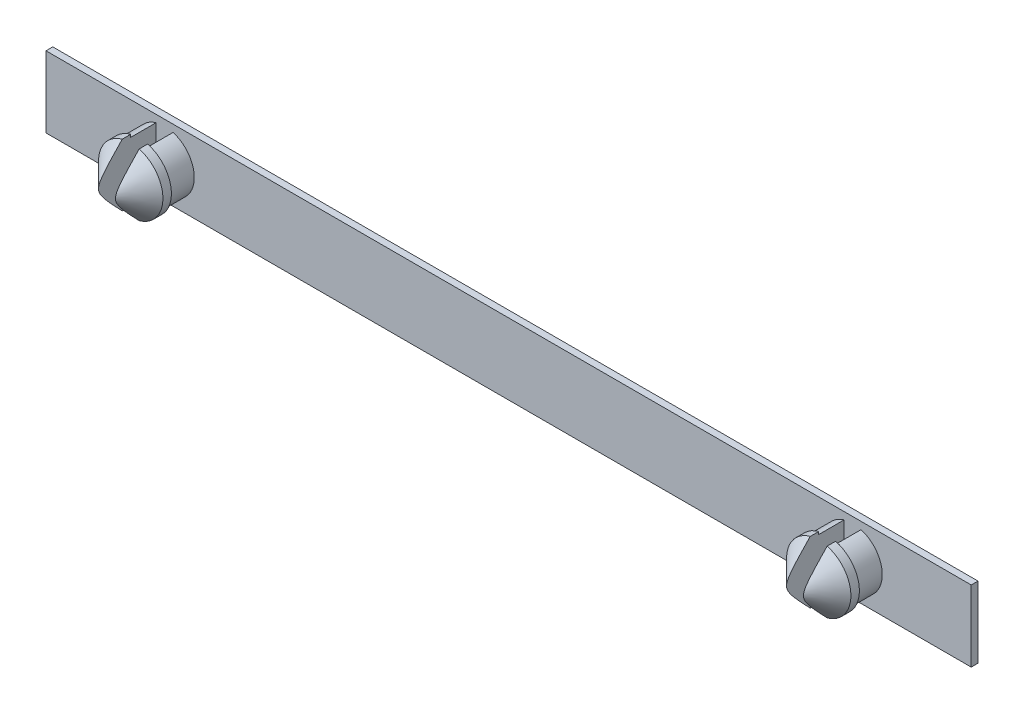
SolidWorks part; units mm, degrees
ref_plane "Přední rovina" through (0, 0, 0) normal (0, 0, 1) x (1, 0, 0)
ref_plane "Horní rovina" through (0, 0, 0) normal (0, 1, 0) x (1, 0, 0)
ref_plane "Pravá rovina" through (0, 0, 0) normal (1, 0, 0) x (0, 0, -1)
sketch "Skica2" plane through (0, 0, 0) normal (0, 0, 1) x (1, 0, 0)
  line L1 (-27.3, 2.1) -> (27.3, 2.1)
  line L2 (-27.3, 2.1) -> (-27.3, -2.1)
  line L3 (-27.3, -2.1) -> (27.3, -2.1)
  line L4 (27.3, 2.1) -> (27.3, -2.1)
  line L5 (-27.3, 2.1) -> (27.3, -2.1) construction
  line L6 (-27.3, -2.1) -> (27.3, 2.1) construction
  point P0 (0, 0)
  point P5 (-1, -0.2)
  dimension "D1" = 4.2
  dimension "D2" = 54.6
extrude "Přidat vysunutím2" add sketch "Skica2" along normal blind 0.4
sketch "Skica3" plane through (0, 0, 0.4) normal (0, 0, 1) x (1, 0, 0)
  line L0 (-27.3, 2.1) -> (-27.3, -2.1) construction
  line L1 (27.3, -2.1) -> (27.3, 2.1) construction
  line L2 (27.3, 2.1) -> (-27.3, 2.1) construction
  line L3 (-27.3, -2.1) -> (27.3, -2.1) construction
  circle A0 centre (-20.3, 0) radius 1.75
  circle A1 centre (20.3, 0) radius 1.75
  dimension "D1" = 3.5
  dimension "D3" = 3.5
  dimension "D2" = 7
  dimension "D4" = 7
  dimension "D5" = 2.1
  dimension "D6" = 2.1
  dimension "D7" = 2.1
extrude "Přidat vysunutím3" add sketch "Skica3" along normal blind 1.5
sketch "Skica5" plane through (0, 0, 1.9) normal (0, 0, 1) x (1, 0, 0)
  circle A0 centre (-20.3, 0) radius 1.9
  circle A1 centre (20.3, 0) radius 1.9
  dimension "D1" = 3.8
  dimension "D2" = 3.8
extrude "Přidat vysunutím5" add sketch "Skica5" along normal blind 2
chamfer "Zkosení2" distance 1.5 angle 45 2 edges at (22.2, 0, 3.9) (-18.4, 0, 3.9)
sketch "Skica7" plane through (0, 0, 3.9) normal (0, 0, 1) x (1, 0, 0)
  line L1 (-19.8, 2.5) -> (-20.8, 2.5)
  line L2 (-19.8, 2.5) -> (-19.8, -2.5)
  line L3 (-19.8, -2.5) -> (-20.8, -2.5)
  line L4 (-20.8, 2.5) -> (-20.8, -2.5)
  line L5 (-19.8, 2.5) -> (-20.8, -2.5) construction
  line L6 (-19.8, -2.5) -> (-20.8, 2.5) construction
  line L7 (19.8, 2.5) -> (20.8, 2.5)
  line L8 (19.8, 2.5) -> (19.8, -2.5)
  line L9 (19.8, -2.5) -> (20.8, -2.5)
  line L10 (20.8, 2.5) -> (20.8, -2.5)
  line L11 (19.8, 2.5) -> (20.8, -2.5) construction
  line L12 (19.8, -2.5) -> (20.8, 2.5) construction
  point P0 (-20.3, 0)
  point P5 (20.3, 0)
  dimension "D1" = 5
  dimension "D2" = 1
  dimension "D3" = 5
  dimension "D4" = 1
extrude "Odebrat vysunutím1" cut sketch "Skica7" against normal blind 3.5
equation "\"1.5.000mm\"=10"
